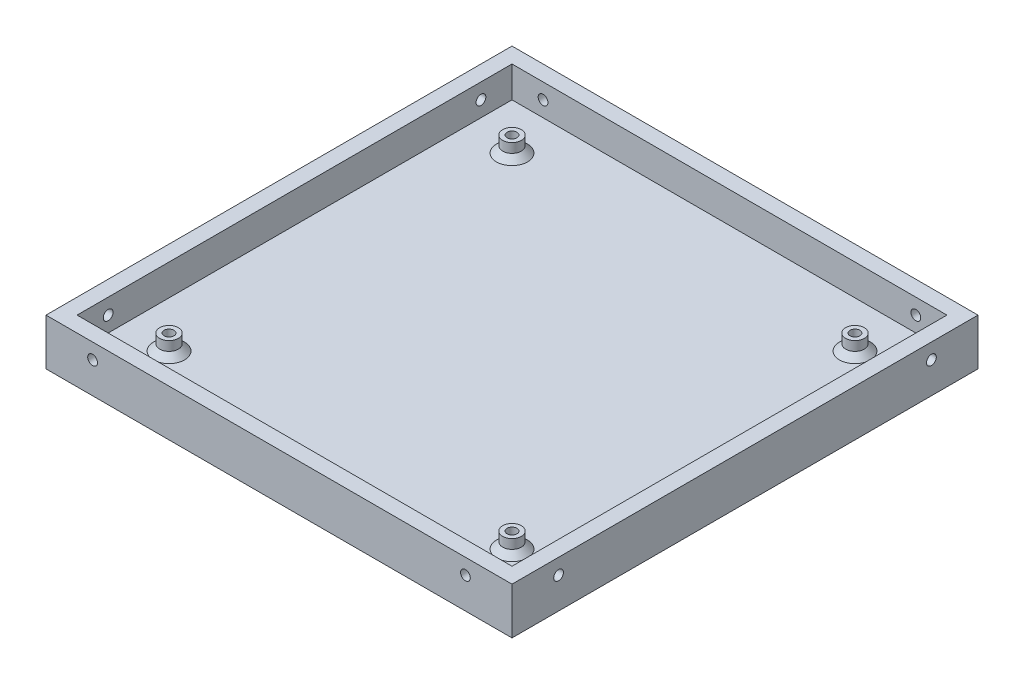
SolidWorks part; units mm, degrees
ref_plane "Front Plane" through (0, 0, 0) normal (0, 0, 1) x (1, 0, 0)
ref_plane "Top Plane" through (0, 0, 0) normal (0, 1, 0) x (1, 0, 0)
ref_plane "Right Plane" through (0, 0, 0) normal (1, 0, 0) x (0, 0, -1)
sketch "Sketch1" plane through (0, 0, 0) normal (0, 1, 0) x (1, 0, 0)
  line L1 (50.8, -50.8) -> (-50.8, -50.8)
  line L2 (50.8, -50.8) -> (50.8, 50.8)
  line L3 (50.8, 50.8) -> (-50.8, 50.8)
  line L4 (-50.8, -50.8) -> (-50.8, 50.8)
  line L5 (50.8, -50.8) -> (-50.8, 50.8) construction
  line L6 (50.8, 50.8) -> (-50.8, -50.8) construction
  point P0 (0, 0)
  dimension "D1" = 101.6
  dimension "D2" = 101.6
extrude "Boss-Extrude1" add sketch "Sketch1" along normal blind 3.175
sketch "Sketch2" plane through (0, 3.175, 0) normal (0, 1, 0) x (1, 0, 0)
  line L1 (-50.8, 50.8) -> (50.8, 50.8)
  line L2 (-50.8, 50.8) -> (-50.8, -50.8)
  line L3 (-50.8, -50.8) -> (50.8, -50.8)
  line L4 (50.8, 50.8) -> (50.8, -50.8)
  line L5 (-44.45, 44.45) -> (44.45, 44.45)
  line L6 (-44.45, 44.45) -> (-44.45, -44.45)
  line L7 (-44.45, -44.45) -> (44.45, -44.45)
  line L8 (44.45, 44.45) -> (44.45, -44.45)
  dimension "D1" = 6.35
  dimension "D2" = 6.35
  dimension "D3" = 6.35
extrude "Boss-Extrude2" add sketch "Sketch2" along normal blind 6.35
ref_axis "Axis1" through (0, 10.0012, 0) along (0, -1, 0)
sketch "Sketch3" plane through (0, 0, 50.8) normal (0, 0, 1) x (1, 0, 0)
  line L1 (-50.8, 9.525) -> (-50.8, 0) construction
  line L2 (-50.8, 9.525) -> (50.8, 9.525) construction
  line L4 (0, 0) -> (0, 9.525) construction
  line L5 (44.45, 9.525) -> (-44.45, 9.525) construction
  line L6 (-50.8, 0) -> (50.8, 0) construction
  circle A0 centre (-38.1, 6.35) radius 0.9995
  circle A2 centre (38.1, 6.35) radius 0.9995
  dimension "D3" = 1.999
  dimension "D1" = 12.7
  dimension "D2" = 3.175
  dimension "D4" = 6.35
extrude "Cut-Extrude1" cut sketch "Sketch3" against normal blind 6.35
pattern_circular "CirPattern1" count 4 over 360 about axis through (0, 10.0012, 0) along (0, -1, 0) of "Cut-Extrude1"
sketch "Sketch4" plane through (0, 0, 0) normal (0, 1, 0) x (1, 0, 0)
  line L1 (-50.8, 50.8) -> (50.8, 50.8)
  line L2 (-50.8, 50.8) -> (-50.8, -50.8)
  line L3 (-50.8, -50.8) -> (50.8, -50.8)
  line L4 (50.8, 50.8) -> (50.8, -50.8)
  line L5 (-47.625, 47.625) -> (47.625, 47.625)
  line L6 (-47.625, 47.625) -> (-47.625, -47.625)
  line L7 (-47.625, -47.625) -> (47.625, -47.625)
  line L8 (47.625, 47.625) -> (47.625, -47.625)
  dimension "D1" = 3.175
  dimension "D2" = 3.175
  dimension "D3" = 3.175
  dimension "D4" = 3.175
extrude "Cut-Extrude2" cut sketch "Sketch4" along normal blind 9.525
sketch "Sketch5" plane through (0, 3.175, 0) normal (0, 1, 0) x (1, 0, 0)
  line L0 (0, 0) -> (0, -38.1) construction
  line L1 (38.1, -38.1) -> (-38.1, -38.1) construction
  line L2 (38.1, -38.1) -> (38.1, 38.1) construction
  line L3 (38.1, 38.1) -> (-38.1, 38.1) construction
  line L4 (-38.1, -38.1) -> (-38.1, 38.1) construction
  line L5 (38.1, -38.1) -> (-38.1, 38.1) construction
  line L6 (38.1, 38.1) -> (-38.1, -38.1) construction
  line L7 (0, 0) -> (38.1, 0) construction
  circle A0 centre (-35.052, -35.052) radius 1.905
  circle A1 centre (-35.052, -35.052) radius 0.9995
  circle A2 centre (35.052, -35.052) radius 1.905
  circle A3 centre (35.052, -35.052) radius 0.9995
  circle A4 centre (35.052, 35.052) radius 1.905
  circle A5 centre (35.052, 35.052) radius 0.9995
  circle A6 centre (-35.052, 35.052) radius 1.905
  circle A7 centre (-35.052, 35.052) radius 0.9995
  point P0 (0, 0)
  dimension "D4" = 3.81
  dimension "D5" = 1.999
  dimension "D1" = 76.2
  dimension "D2" = 76.2
  dimension "D3" = 3.048
extrude "Boss-Extrude3" add sketch "Sketch5" along normal blind 3.175
sketch "Sketch6" plane through (0, 6.35, 0) normal (0, 1, 0) x (1, 0, 0)
  circle A0 centre (-35.052, 35.052) radius 0.9995
  circle A1 centre (35.052, 35.052) radius 0.9995
  circle A2 centre (35.052, -35.052) radius 0.9995
  circle A3 centre (-35.052, -35.052) radius 0.9995
extrude "Cut-Extrude3" cut sketch "Sketch6" against normal through all
chamfer "Chamfer1" distance 1.27 angle 45 4 edges at (-35.052, 0, -34.0525) (-35.052, 0, 36.0515) (35.052, 0, 36.0515) (35.052, 0, -34.0525)
chamfer "Chamfer2" distance 1.27 angle 45 4 edges at (-35.052, 3.175, -36.957) (35.052, 3.175, 33.147) (-35.052, 3.175, 36.957) (35.052, 3.175, -33.147)
